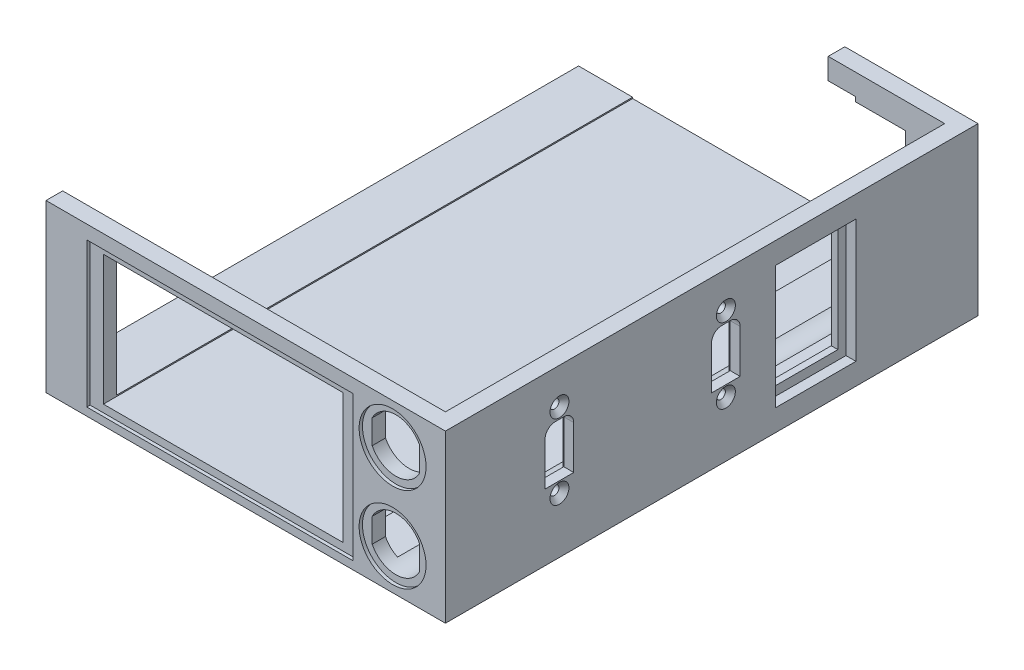
SolidWorks part; units mm, degrees
ref_plane "Front Plane" through (0, 0, 0) normal (0, 0, 1) x (1, 0, 0)
ref_plane "Top Plane" through (0, 0, 0) normal (0, 1, 0) x (1, 0, 0)
ref_plane "Right Plane" through (0, 0, 0) normal (1, 0, 0) x (0, 0, -1)
sketch "Sketch1" plane through (0, 0, 0) normal (0, 0, 1) x (1, 0, 0)
  line L1 (-60, -25) -> (60, -25)
  line L2 (-60, -25) -> (-60, 25)
  line L3 (-60, 25) -> (60, 25)
  line L4 (60, -25) -> (60, 25)
  line L5 (-60, -25) -> (60, 25) construction
  line L6 (-60, 25) -> (60, -25) construction
  point P0 (0, 0)
  dimension "D1" = 120
  dimension "D2" = 50
extrude "Boss-Extrude1" add sketch "Sketch1" against normal blind 160
shell "Shell1" thickness 5
sketch "Sketch4" plane through (0, 0, 0) normal (0, 0, 1) x (1, 0, 0)
  line L0 (28.2472, 12.8166) -> (60, 12.8166) construction
  line L1 (-43.7528, 18.6352) -> (28.2472, 18.6352)
  line L2 (-43.7528, 18.6352) -> (-43.7528, -20.3648)
  line L3 (-43.7528, -20.3648) -> (28.2472, -20.3648)
  line L4 (28.2472, 18.6352) -> (28.2472, -20.3648)
  line L5 (-43.7528, 18.6352) -> (28.2472, -20.3648) construction
  line L6 (-43.7528, -20.3648) -> (28.2472, 18.6352) construction
  line L7 (60, -25) -> (60, 25) construction
  circle A3 centre (44.1236, 12.8166) radius 7.1 construction
  point P0 (-7.7528, -0.8648)
  dimension "D3" = 14.2
  dimension "D1" = 39
  dimension "D2" = 72
extrude "Cut-Extrude2" cut sketch "Sketch4" against normal up to next
sketch "Sketch5" plane through (0, 0, 0) normal (0, 0, 1) x (1, 0, 0)
  line L1 (-47.7528, -22.6148) -> (32.2472, -22.6148)
  line L2 (-47.7528, -22.6148) -> (-47.7528, 20.8852)
  line L3 (-47.7528, 20.8852) -> (32.2472, 20.8852)
  line L4 (32.2472, -22.6148) -> (32.2472, 20.8852)
  line L5 (-47.7528, -22.6148) -> (32.2472, 20.8852) construction
  line L6 (-47.7528, 20.8852) -> (32.2472, -22.6148) construction
  point P0 (-7.7528, -0.8648)
  dimension "D1" = 80
  dimension "D2" = 43.5
extrude "Cut-Extrude3" cut sketch "Sketch5" against normal blind 1
sketch "Sketch6" plane through (0, 0, 0) normal (0, 0, 1) x (1, 0, 0)
  line L0 (51.2562, 9.1937) -> (51.2562, 16.4394)
  line L1 (36.9909, 16.4394) -> (36.9909, 9.1937)
  arc A0 (36.9909, 9.1937) -> (51.2562, 9.1937) centre (44.1236, 12.8166) ccw
  arc A1 (51.2562, 16.4394) -> (36.9909, 16.4394) centre (44.1236, 12.8166) ccw
  point P1 (32.9206, 11.3038)
  dimension "D1" = 8
extrude "Cut-Extrude4" cut sketch "Sketch6" against normal up to next
sketch "Sketch7" plane through (0, 0, 0) normal (0, 0, 1) x (1, 0, 0)
  circle A0 centre (44.1236, 12.8166) radius 10.0549
extrude "Cut-Extrude5" cut sketch "Sketch7" against normal blind 1
mirror "Mirror1" about plane through (0, 0, 0) normal (0, 1, 0) of "Cut-Extrude5", "Cut-Extrude4"
sketch "Sketch9" plane through (60, 0, 0) normal (1, 0, 0) x (0, 0, -1)
  line L0 (34.2504, 2.9528) -> (43.0138, 2.9528) construction
  line L1 (29.9504, -5.0472) -> (38.5504, -5.0472)
  line L2 (29.9504, -5.0472) -> (29.9504, 7.9528)
  line L3 (32.9504, 10.9528) -> (35.5504, 10.9528)
  line L4 (38.5504, -5.0472) -> (38.5504, 7.9528)
  line L5 (34.2504, 2.9528) -> (34.2504, 14.2028) construction
  arc A0 (35.5504, 10.9528) -> (38.5504, 7.9528) centre (35.5504, 7.9528) cw
  arc A1 (29.9504, 7.9528) -> (32.9504, 10.9528) centre (32.9504, 7.9528) cw
  circle A2 centre (34.2504, 14.2028) radius 1.35
  circle A3 centre (34.2504, -8.2972) radius 1.35
  point P12 (34.2504, -5.0472)
  dimension "D1" = 3
  dimension "D5" = 2.7
  dimension "D2" = 8.6
  dimension "D3" = 16
  dimension "D4" = 11.25
extrude "Cut-Extrude6" cut sketch "Sketch9" against normal up to next
chamfer "Chamfer1" distance 1.5 angle 45 2 edges at (60, -8.2972, -32.9004) (60, 14.2028, -35.6004)
sketch "Sketch10" plane through (55, 0, 0) normal (-1, 0, 0) x (0, 0, 1)
  line L1 (-40.2504, -11.0472) -> (-28.2504, -11.0472)
  line L2 (-40.2504, -11.0472) -> (-40.2504, 16.9528)
  line L3 (-40.2504, 16.9528) -> (-28.2504, 16.9528)
  line L4 (-28.2504, -11.0472) -> (-28.2504, 16.9528)
  line L5 (-40.2504, -11.0472) -> (-28.2504, 16.9528) construction
  line L6 (-40.2504, 16.9528) -> (-28.2504, -11.0472) construction
  point P0 (-34.2504, 2.9528)
  dimension "D1" = 12
  dimension "D2" = 28
extrude "Cut-Extrude7" cut sketch "Sketch10" against normal offset from surface (2 mm away) 3 up to face at (60, -8.2972, -37.1004)
pattern_linear "LPattern1" count 2 spacing 50 along (0, 0, -1) of "Cut-Extrude6", "Cut-Extrude7", "Chamfer1"
sketch "Sketch11" plane through (60, 0, 0) normal (1, 0, 0) x (0, 0, -1)
  line L1 (101.6308, -15.7589) -> (120.9185, -15.7589)
  line L2 (101.6308, -15.7589) -> (101.6308, 15.7589)
  line L3 (101.6308, 15.7589) -> (120.9185, 15.7589)
  line L4 (120.9185, -15.7589) -> (120.9185, 15.7589)
  line L5 (101.6308, -15.7589) -> (120.9185, 15.7589) construction
  line L6 (101.6308, 15.7589) -> (120.9185, -15.7589) construction
  point P0 (111.2747, 0)
extrude "Cut-Extrude8" cut sketch "Sketch11" against normal through all
sketch "Sketch12" plane through (60, 0, 0) normal (1, 0, 0) x (0, 0, -1)
  line L1 (99.2266, -18.5168) -> (123.3227, -18.5168)
  line L2 (99.2266, -18.5168) -> (99.2266, 18.5168)
  line L3 (99.2266, 18.5168) -> (123.3227, 18.5168)
  line L4 (123.3227, -18.5168) -> (123.3227, 18.5168)
  line L5 (99.2266, -18.5168) -> (123.3227, 18.5168) construction
  line L6 (99.2266, 18.5168) -> (123.3227, -18.5168) construction
  point P0 (111.2747, 0)
extrude "Cut-Extrude9" cut sketch "Sketch12" against normal blind 3
sketch "Sketch13" plane through (0, 0, -160) normal (0, 0, -1) x (-1, 0, 0)
  line L1 (-43.167, -17.268) -> (-18.5649, -17.268)
  line L2 (-43.167, -17.268) -> (-43.167, 17.268)
  line L3 (-43.167, 17.268) -> (-18.5649, 17.268)
  line L4 (-18.5649, -17.268) -> (-18.5649, 17.268)
  line L5 (-43.167, -17.268) -> (-18.5649, 17.268) construction
  line L6 (-43.167, 17.268) -> (-18.5649, -17.268) construction
  point P0 (-30.866, 0)
extrude "Cut-Extrude10" cut sketch "Sketch13" against normal up to next
sketch "Sketch2" plane through (0, -20, 0) normal (0, 1, 0) x (1, 0, 0)
  line L0 (-60, 155) -> (-43.7528, 155) construction
  line L1 (20, 155) -> (-60, 155)
  line L2 (20, 155) -> (20, 212.5209)
  line L3 (20, 212.5209) -> (-60, 212.5209)
  line L4 (-60, 155) -> (-60, 212.5209)
  line L5 (-60, 155) -> (-60, 5) construction
  dimension "D1" = 35
extrude "Cut-Extrude1" cut sketch "Sketch2" along normal through all
